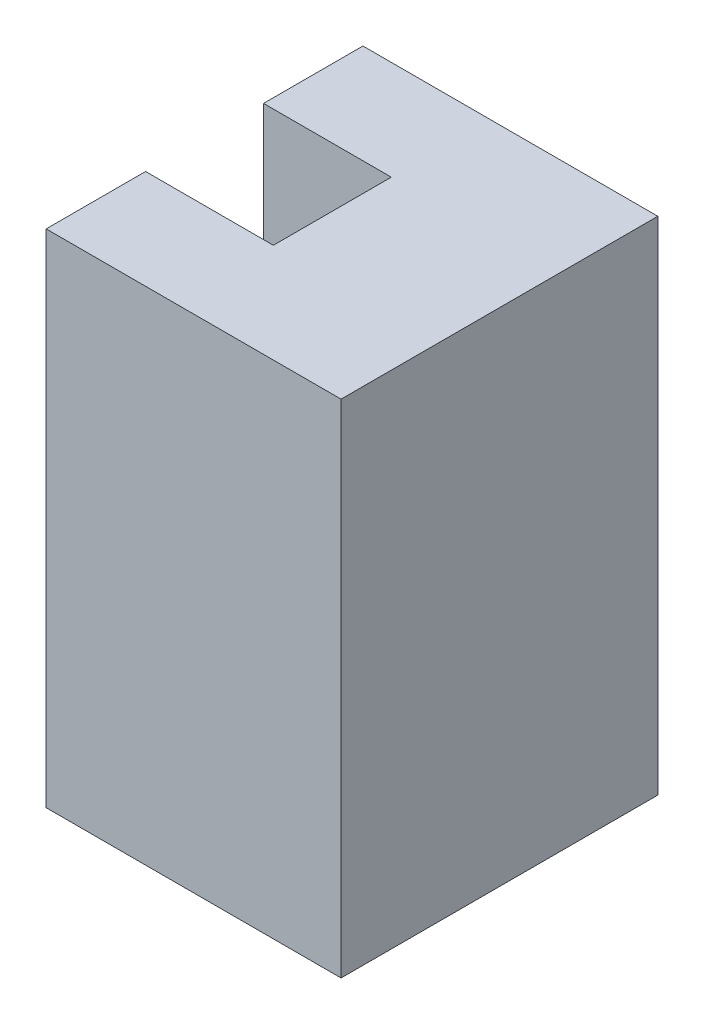
SolidWorks part; units mm, degrees
ref_plane "Front Plane" through (0, 0, 0) normal (0, 0, 1) x (1, 0, 0)
ref_plane "Top Plane" through (0, 0, 0) normal (0, 1, 0) x (1, 0, 0)
ref_plane "Right Plane" through (0, 0, 0) normal (1, 0, 0) x (0, 0, -1)
sketch "Sketch1" plane through (0, 0, 0) normal (0, 1, 0) x (1, 0, 0)
  line L0 (0, 5.5563) -> (0, 8.0563)
  line L1 (6.4158, 0) -> (3.2079, 5.5563)
  line L2 (3.2079, 5.5563) -> (0, 5.5563)
  line L5 (0, -5.5563) -> (3.2079, -5.5563)
  line L6 (3.2079, -5.5563) -> (6.4158, 0)
  line L7 (0, 8.0563) -> (15, 8.0562)
  line L8 (15, 8.0562) -> (15, -8.0562)
  line L9 (15, -8.0562) -> (0, -8.0562)
  line L10 (0, -8.0562) -> (0, -5.5563)
  line L12 (-4.8119, -2.7781) -> (-3.2079, -5.5563) [skipped]
  line L13 (-3.2079, 5.5563) -> (-4.8119, 2.7781) [skipped]
  circle A0 centre (0, 0) radius 5.5562 construction
  dimension "D1" = 11.1125
  dimension "D2" = 2.5
  dimension "D3" = 2.5
  dimension "D4" = 15
extrude "Boss-Extrude1" add sketch "Sketch1" along normal blind 5.5
sketch "Sketch2" plane through (0, 5.5, 0) normal (0, 1, 0) x (1, 0, 0)
  line L0 (15, -8.0562) -> (15, 8.0562) construction
  line L1 (0, 8.0563) -> (15, 8.0563)
  line L2 (0, 8.0563) -> (0, -8.0562)
  line L3 (0, -8.0562) -> (15, -8.0562)
  line L4 (15, 8.0563) -> (15, -8.0562)
extrude "Boss-Extrude2" add sketch "Sketch2" along normal blind 20
sketch "Sketch3" plane through (0, 0, 0) normal (-1, 0, 0) x (0, 0, 1)
  line L0 (-8.0563, 25.5) -> (8.0562, 25.5) construction
  line L1 (-3, 25.5) -> (3, 25.5)
  line L2 (-3, 25.5) -> (-3, 7.5)
  line L3 (-3, 7.5) -> (3, 7.5)
  line L4 (3, 25.5) -> (3, 7.5)
  line L5 (0, 25.5) -> (0, 0) construction
  dimension "D1" = 6
  dimension "D2" = 18
extrude "Cut-Extrude1" cut sketch "Sketch3" against normal blind 6.5
